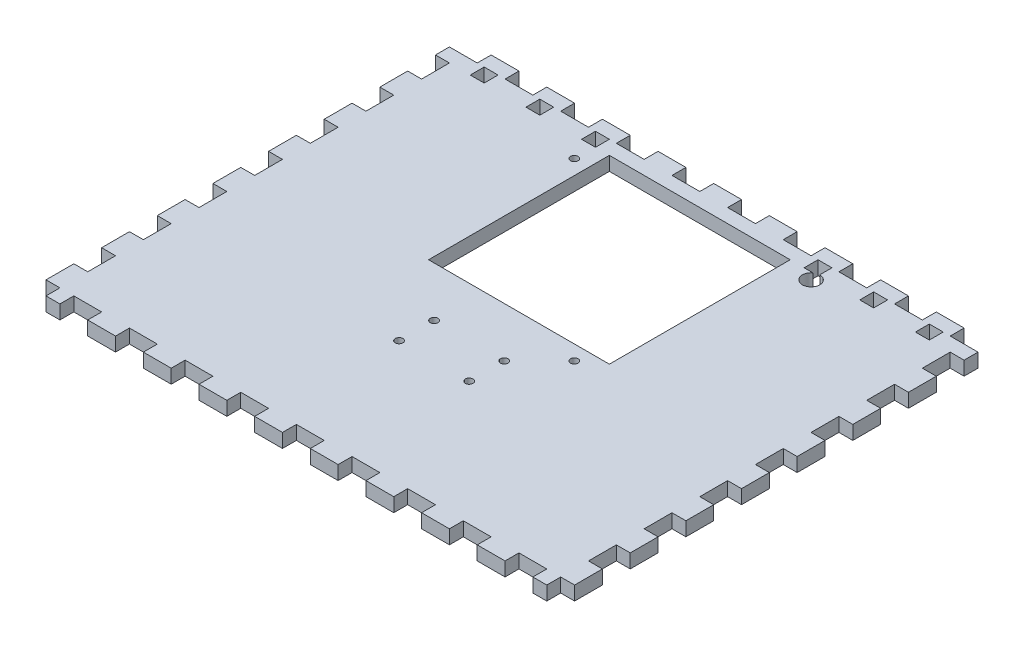
SolidWorks part; units mm, degrees
material "Pine"
ref_plane "Front Plane" through (0, 0, 0) normal (0, 0, 1) x (1, 0, 0)
ref_plane "Top Plane" through (0, 0, 0) normal (0, 1, 0) x (1, 0, 0)
ref_plane "Right Plane" through (0, 0, 0) normal (1, 0, 0) x (0, 0, -1)
sketch "Sketch1" plane through (0, 0, 0) normal (0, 1, 0) x (1, 0, 0)
  line L1 (0, 0) -> (241.3, 0)
  line L2 (0, 0) -> (0, 254)
  line L3 (0, 254) -> (241.3, 254)
  line L4 (241.3, 0) -> (241.3, 254)
  dimension "D1" = 241.3
  dimension "D2" = 254
extrude "Boss-Extrude1" add sketch "Sketch1" along normal blind 6.35
sketch "Sketch2" plane through (0, 6.35, 0) normal (0, 1, 0) x (1, 0, 0)
  line L1 (0, 12.7) -> (6.35, 12.7)
  line L2 (0, 12.7) -> (0, 0)
  line L3 (0, 0) -> (6.35, 0)
  line L4 (6.35, 12.7) -> (6.35, 0)
  line L5 (241.3, 12.7) -> (234.95, 12.7)
  line L6 (241.3, 12.7) -> (241.3, 0)
  line L7 (241.3, 0) -> (234.95, 0)
  line L8 (234.95, 12.7) -> (234.95, 0)
  dimension "D1" = 12.7
  dimension "D2" = 6.35
extrude "Cut-Extrude1" cut sketch "Sketch2" against normal through all
pattern_linear "LPattern1" count 10 spacing 25.4 along (0, 0, -1) of "Cut-Extrude1"
sketch "Sketch3" plane through (0, 6.35, 0) normal (0, 1, 0) x (1, 0, 0)
  line L0 (6.35, 0) -> (234.95, 0) construction
  line L1 (0, 0) -> (12.7, 0)
  line L2 (0, 0) -> (0, 6.35)
  line L3 (0, 6.35) -> (12.7, 6.35)
  line L4 (12.7, 0) -> (12.7, 6.35)
  line L5 (241.3, 254) -> (0, 254) construction
  line L6 (0, 254) -> (12.7, 254)
  line L7 (0, 254) -> (0, 247.65)
  line L8 (0, 247.65) -> (12.7, 247.65)
  line L9 (12.7, 254) -> (12.7, 247.65)
  dimension "D2" = 12.7
  dimension "D3" = 6.35
extrude "Cut-Extrude2" cut sketch "Sketch3" against normal through all
pattern_linear "LPattern2" count 10 spacing 25.4 along (1, 0, 0) of "Cut-Extrude2"
sketch "Sketch4" plane through (0, 6.35, 0) normal (0, 1, 0) x (1, 0, 0)
  line L0 (241.3, 12.7) -> (241.3, 25.4) construction
  line L1 (0, 57.15) -> (241.3, 57.15)
  line L2 (0, 57.15) -> (0, 0)
  line L3 (0, 0) -> (241.3, 0)
  line L4 (241.3, 57.15) -> (241.3, 0)
  line L5 (12.7, 0) -> (25.4, 0) construction
  line L6 (0, 50.8) -> (0, 38.1) construction
  line L7 (6.35, 63.5) -> (0, 63.5) construction
  dimension "D1" = 6.35
extrude "Cut-Extrude3" cut sketch "Sketch4" against normal through all
sketch "Sketch5" plane through (0, 6.35, 0) normal (0, 1, 0) x (1, 0, 0)
  line L0 (234.95, 57.15) -> (6.35, 57.15) construction
  line L1 (12.7, 57.15) -> (25.4, 57.15)
  line L2 (12.7, 57.15) -> (12.7, 63.5)
  line L3 (12.7, 63.5) -> (25.4, 63.5)
  line L4 (25.4, 57.15) -> (25.4, 63.5)
  line L5 (12.7, 247.65) -> (12.7, 254) construction
  line L6 (6.35, 76.2) -> (6.35, 88.9) construction
extrude "Cut-Extrude4" cut sketch "Sketch5" against normal through all
pattern_linear "LPattern3" count 10 spacing 25.4 along (1, 0, 0) of "Cut-Extrude4"
sketch "Sketch6" plane through (0, 6.35, 0) normal (0, 1, 0) x (1, 0, 0)
  line L0 (0, 127) -> (0, 114.3) construction
  line L1 (79.375, 241.3) -> (161.925, 241.3)
  line L2 (79.375, 241.3) -> (79.375, 158.75)
  line L3 (79.375, 158.75) -> (161.925, 158.75)
  line L4 (161.925, 241.3) -> (161.925, 158.75)
  line L6 (101.6, 247.65) -> (114.3, 247.65) construction
  dimension "D1" = 82.55
  dimension "D2" = 82.55
  dimension "D3" = 79.375
  dimension "D4" = 6.35
extrude "Cut-Extrude5" cut sketch "Sketch6" against normal through all
sketch "Sketch7" plane through (0, 6.35, 0) normal (0, 1, 0) x (1, 0, 0)
  line L0 (19.05, 254) -> (19.05, 244.475) construction
  line L1 (25.4, 254) -> (12.7, 254) construction
  line L3 (15.875, 247.65) -> (22.225, 247.65)
  line L4 (15.875, 247.65) -> (15.875, 241.3)
  line L5 (15.875, 241.3) -> (22.225, 241.3)
  line L6 (22.225, 247.65) -> (22.225, 241.3)
  line L7 (15.875, 247.65) -> (22.225, 241.3) construction
  line L8 (15.875, 241.3) -> (22.225, 247.65) construction
  dimension "D1" = 6.35
  dimension "D2" = 6.35
  dimension "D3" = 9.525
extrude "Cut-Extrude6" cut sketch "Sketch7" against normal through all
pattern_linear "LPattern4" count 9 spacing 25.4 along (1, 0, 0) skipping (3, 0), (4, 0), (5, 0) of "Cut-Extrude6"
sketch "Sketch8" plane through (0, 6.35, 0) normal (0, 1, 0) x (1, 0, 0)
  line L2 (79.375, 241.3) -> (79.375, 158.75) construction
  line L3 (79.375, 158.75) -> (161.925, 158.75) construction
  line L5 (72.65, 152.025) -> (24.65, 152.025) construction
  line L6 (72.65, 152.025) -> (72.65, 72.025) construction
  line L7 (72.65, 72.025) -> (24.65, 72.025) construction
  line L8 (24.65, 152.025) -> (24.65, 72.025) construction
  circle A0 centre (72.65, 152.025) radius 1.75 construction
  circle A1 centre (24.65, 72.025) radius 1.75
  dimension "D3" = 3.5
  dimension "D1" = 6.725
  dimension "D2" = 6.725
  dimension "D4" = 48
  dimension "D5" = 80
extrude "Cut-Extrude7" cut sketch "Sketch8" against normal through all
pattern_linear "LPattern5" count 13 spacing 16 along (1, 0, 0) count 11 spacing 16 along (0, 0, -1) of "Cut-Extrude7"
sketch "Sketch9" plane through (0, 6.35, 0) normal (0, 1, 0) x (1, 0, 0)
  line L0 (79.375, 241.3) -> (79.375, 158.75) construction
  line L1 (14.3867, 236.0841) -> (62.4324, 236.0841)
  line L2 (14.3867, 236.0841) -> (14.3867, 69.0061)
  line L3 (14.3867, 69.0061) -> (62.4324, 69.0061)
  line L4 (62.4324, 236.0841) -> (62.4324, 69.0061)
  line L5 (226.9133, 236.0841) -> (180.599, 236.0841)
  line L6 (226.9133, 236.0841) -> (226.9133, 69.0061)
  line L7 (226.9133, 69.0061) -> (180.599, 69.0061)
  line L8 (180.599, 236.0841) -> (180.599, 69.0061)
  line L9 (67.6265, 69.0061) -> (176.2705, 69.0061)
  line L10 (67.6265, 69.0061) -> (67.6265, 110.1263)
  line L11 (67.6265, 110.1263) -> (176.2705, 110.1263)
  line L12 (176.2705, 69.0061) -> (176.2705, 110.1263)
  line L14 (67.6265, 140.1099) -> (98.9107, 140.1099)
  line L15 (67.6265, 140.1099) -> (67.6265, 131.4876)
  line L16 (67.6265, 131.4876) -> (98.9107, 131.4876)
  line L17 (67.6265, 115.3205) -> (93.5972, 115.3205)
  line L18 (67.6265, 115.3205) -> (67.6265, 125.7087)
  line L19 (67.6265, 125.7087) -> (93.5972, 125.7087)
  line L20 (93.5972, 115.3205) -> (93.5972, 125.7087)
  line L21 (115.2394, 115.3205) -> (130.389, 115.3205)
  line L22 (115.2394, 115.3205) -> (115.2394, 125.7087)
  line L23 (115.2394, 125.7087) -> (130.389, 125.7087)
  line L24 (130.389, 115.3205) -> (130.389, 125.7087)
  line L25 (145.5386, 115.3205) -> (176.2705, 115.3205)
  line L26 (145.5386, 115.3205) -> (145.5386, 125.7087)
  line L27 (145.5386, 125.7087) -> (176.2705, 125.7087)
  line L28 (176.2705, 115.3205) -> (176.2705, 125.7087)
  line L29 (67.6265, 156.0078) -> (141.2101, 156.0078)
  line L30 (67.6265, 156.0078) -> (67.6265, 147.351)
  line L31 (67.6265, 147.351) -> (141.2101, 147.351)
  line L32 (141.2101, 156.0078) -> (141.2101, 147.351)
  line L33 (161.9867, 147.351) -> (176.2705, 147.351)
  line L34 (161.9867, 147.351) -> (161.9867, 156.0078)
  line L35 (161.9867, 156.0078) -> (176.2705, 156.0078)
  line L36 (176.2705, 147.351) -> (176.2705, 156.0078)
  line L37 (173.2406, 163.799) -> (165.0166, 163.799)
  line L38 (173.2406, 163.799) -> (173.2406, 236.0841)
  line L39 (173.2406, 236.0841) -> (165.0166, 236.0841)
  line L40 (165.0166, 163.799) -> (165.0166, 236.0841)
  line L41 (79.375, 163.799) -> (67.6265, 163.799)
  line L42 (79.375, 163.799) -> (79.375, 223.5316)
  line L43 (79.375, 223.5316) -> (67.6265, 223.5316)
  line L44 (67.6265, 163.799) -> (67.6265, 223.5316)
  line L45 (98.9107, 140.1099) -> (98.9107, 131.4876)
  line L46 (115.2394, 140.1099) -> (124.4182, 140.1099)
  line L47 (115.2394, 140.1099) -> (115.2394, 131.4876)
  line L48 (115.2394, 131.4876) -> (124.4182, 131.4876)
  line L49 (124.4182, 140.1099) -> (124.4182, 131.4876)
  line L50 (149.2072, 140.1099) -> (176.2705, 140.1099)
  line L51 (149.2072, 140.1099) -> (149.2072, 131.4876)
  line L52 (149.2072, 131.4876) -> (176.2705, 131.4876)
  line L53 (176.2705, 140.1099) -> (176.2705, 131.4876)
extrude "Boss-Extrude2" add sketch "Sketch9" against normal through all
sketch "Sketch10" plane through (0, 6.35, 0) normal (0, 1, 0) x (1, 0, 0)
  circle A0 centre (174.625, 238.125) radius 3.9688
  circle A1 centre (174.625, 238.125) radius 3.9688 construction
extrude "Cut-Extrude8" cut sketch "Sketch10" against normal through all
